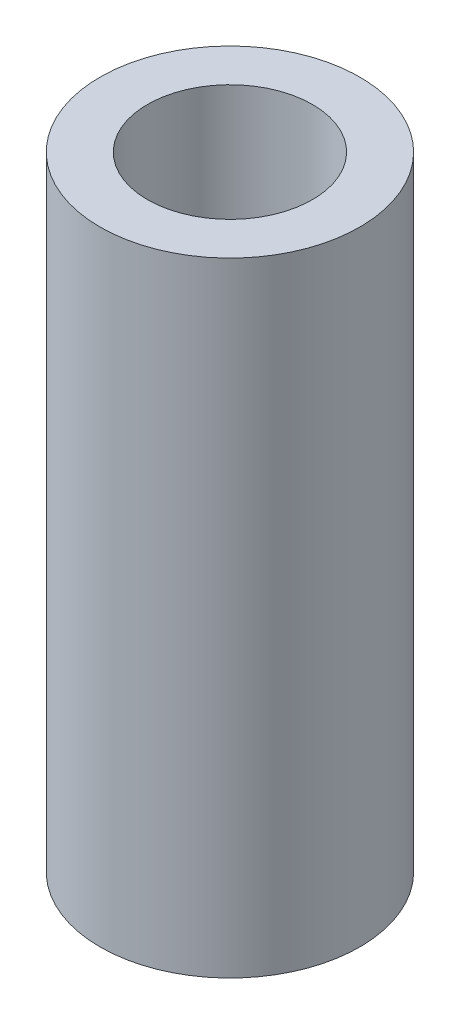
SolidWorks part; units mm, degrees
ref_plane "Front Plane" through (0, 0, 0) normal (0, 0, 1) x (1, 0, 0)
ref_plane "Top Plane" through (0, 0, 0) normal (0, 1, 0) x (1, 0, 0)
ref_plane "Right Plane" through (0, 0, 0) normal (1, 0, 0) x (0, 0, -1)
sketch "Sketch2" plane through (0, 0, 0) normal (0, 1, 0) x (1, 0, 0)
  circle A0 centre (0, 0) radius 3.9688
  dimension "D1" = 7.9375
extrude "Boss-Extrude1" add sketch "Sketch2" along normal blind 19.05
sketch "Sketch3" plane through (0, 19.05, 0) normal (0, 1, 0) x (1, 0, 0)
  circle A0 centre (0, 0) radius 2.521
  dimension "D1" = 5.0419
extrude "Cut-Extrude1" cut sketch "Sketch3" against normal through all both and the other way through all
